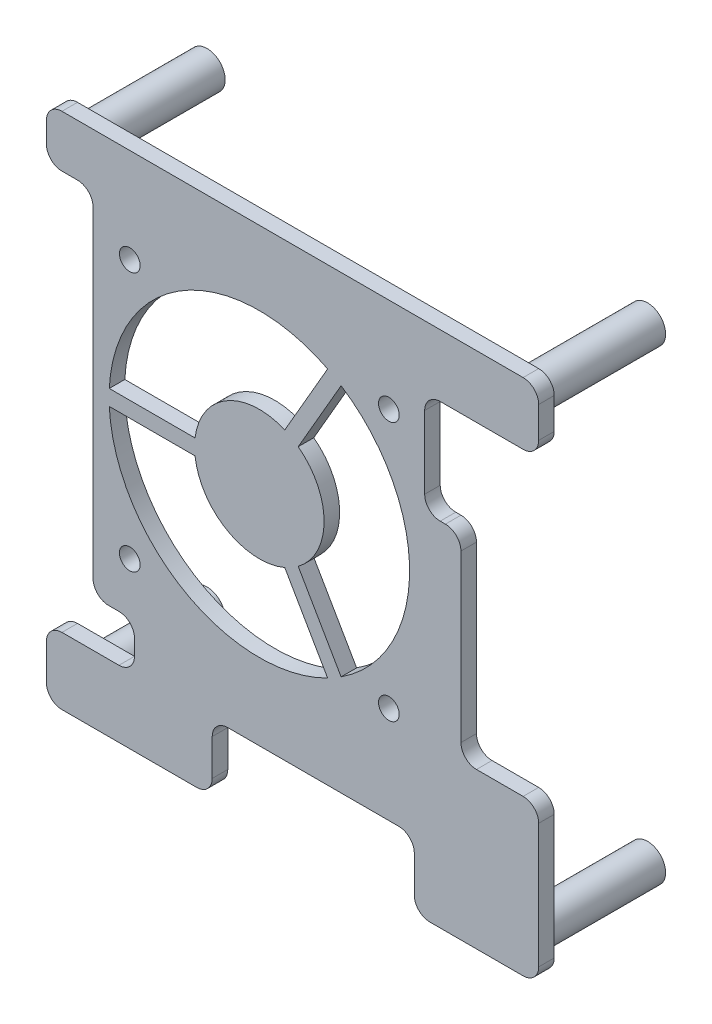
SolidWorks part; units mm, degrees
ref_plane "Alzado" through (0, 0, 0) normal (0, 0, 1) x (1, 0, 0)
ref_plane "Planta" through (0, 0, 0) normal (0, 1, 0) x (1, 0, 0)
ref_plane "Vista lateral" through (0, 0, 0) normal (1, 0, 0) x (0, 0, -1)
sketch "Croquis1" plane through (0, 0, 0) normal (0, 0, 1) x (1, 0, 0)
  line L0 (-194.105, 92.4709) -> (-194.105, 88.4709)
  line L1 (-191.105, 95.4709) -> (-102.105, 95.4709)
  line L2 (-99.105, 92.4709) -> (-99.105, 86.4709)
  line L3 (-140.5125, 52.2157) -> (-124.0125, 52.2157) construction
  line L4 (-102.105, -4.5291) -> (-120.105, -4.5291)
  line L5 (-194.105, 95.4709) -> (-99.105, -4.5291) construction
  line L6 (-194.105, -4.5291) -> (-99.105, 95.4709) construction
  line L7 (-191.105, 85.4709) -> (-188.105, 85.4709)
  line L8 (-185.105, 82.4709) -> (-185.105, 20.3828)
  line L9 (-182.105, 17.3828) -> (-180.105, 17.3828)
  line L10 (-177.105, 14.3828) -> (-177.105, 11.3828)
  line L11 (-180.105, 8.3828) -> (-191.105, 8.3828)
  line L12 (-194.105, 5.3828) -> (-194.105, -1.5291)
  line L13 (-102.105, 83.4709) -> (-118.105, 83.4709)
  line L14 (-121.105, 80.4709) -> (-121.105, 66.4709)
  line L15 (-118.105, 63.4709) -> (-117.105, 63.4709)
  line L16 (-114.105, 60.4709) -> (-114.105, 28.4709)
  line L17 (-111.105, 25.4709) -> (-102.105, 25.4709)
  line L18 (-99.105, 22.4709) -> (-99.105, -1.5291)
  line L19 (-123.105, -1.5291) -> (-123.105, 5.4709)
  line L20 (-126.105, 8.4709) -> (-159.105, 8.4709)
  line L21 (-162.105, 5.4709) -> (-162.105, -1.5291)
  line L22 (-165.105, -4.5291) -> (-191.105, -4.5291)
  line L27 (-183.0125, 82.2157) -> (-123.0125, 22.2157) construction
  line L28 (-183.0125, 22.2157) -> (-123.0125, 82.2157) construction
  line L29 (-132.2625, 52.2157) -> (-132.2625, 53.7157) construction
  line L30 (-165.4222, 50.7157) -> (-181.9737, 50.7157)
  line L31 (-132.2625, 52.2157) -> (-132.2625, 50.7157) construction
  line L32 (-165.4222, 53.7157) -> (-181.9737, 53.7157)
  line L33 (-145.5086, 62.2128) -> (-137.2329, 76.5468)
  line L34 (-148.1067, 63.7128) -> (-139.831, 78.0468)
  line L35 (-148.1067, 40.7186) -> (-139.831, 26.3846)
  line L36 (-145.5086, 42.2186) -> (-137.2329, 27.8846)
  arc A0 (-194.105, 92.4709) -> (-191.105, 95.4709) centre (-191.105, 92.4709) cw
  arc A1 (-194.105, 88.4709) -> (-191.105, 85.4709) centre (-191.105, 88.4709) ccw
  arc A2 (-185.105, 82.4709) -> (-188.105, 85.4709) centre (-188.105, 82.4709) ccw
  arc A3 (-182.105, 17.3828) -> (-185.105, 20.3828) centre (-182.105, 20.3828) cw
  arc A4 (-177.105, 14.3828) -> (-180.105, 17.3828) centre (-180.105, 14.3828) ccw
  arc A5 (-177.105, 11.3828) -> (-180.105, 8.3828) centre (-180.105, 11.3828) cw
  arc A6 (-191.105, 8.3828) -> (-194.105, 5.3828) centre (-191.105, 5.3828) ccw
  arc A7 (-194.105, -1.5291) -> (-191.105, -4.5291) centre (-191.105, -1.5291) ccw
  arc A8 (-162.105, -1.5291) -> (-165.105, -4.5291) centre (-165.105, -1.5291) cw
  arc A9 (-159.105, 8.4709) -> (-162.105, 5.4709) centre (-159.105, 5.4709) ccw
  arc A10 (-123.105, 5.4709) -> (-126.105, 8.4709) centre (-126.105, 5.4709) ccw
  arc A11 (-120.105, -4.5291) -> (-123.105, -1.5291) centre (-120.105, -1.5291) cw
  arc A12 (-102.105, -4.5291) -> (-99.105, -1.5291) centre (-102.105, -1.5291) ccw
  arc A13 (-102.105, 25.4709) -> (-99.105, 22.4709) centre (-102.105, 22.4709) cw
  arc A14 (-114.105, 28.4709) -> (-111.105, 25.4709) centre (-111.105, 28.4709) ccw
  arc A15 (-117.105, 63.4709) -> (-114.105, 60.4709) centre (-117.105, 60.4709) cw
  arc A16 (-121.105, 66.4709) -> (-118.105, 63.4709) centre (-118.105, 66.4709) ccw
  arc A17 (-118.105, 83.4709) -> (-121.105, 80.4709) centre (-118.105, 80.4709) ccw
  arc A18 (-99.105, 86.4709) -> (-102.105, 83.4709) centre (-102.105, 86.4709) cw
  arc A19 (-102.105, 95.4709) -> (-99.105, 92.4709) centre (-102.105, 92.4709) cw
  arc A21 (-181.9737, 53.7157) -> (-139.831, 78.0468) centre (-153.0125, 52.2157) cw
  arc A22 (-165.4222, 53.7157) -> (-148.1067, 63.7128) centre (-153.0125, 52.2157) cw
  arc A23 (-145.5086, 62.2128) -> (-145.5086, 42.2186) centre (-153.0125, 52.2157) cw
  arc A24 (-148.1067, 40.7186) -> (-165.4222, 50.7157) centre (-153.0125, 52.2157) cw
  arc A25 (-137.2329, 76.5468) -> (-137.2329, 27.8846) centre (-153.0125, 52.2157) cw
  arc A26 (-139.831, 26.3846) -> (-181.9737, 50.7157) centre (-153.0125, 52.2157) cw
  point P0 (-146.605, 45.4709)
  point P65 (-153.0125, 52.2157)
  point P92 (-153.0125, 52.2157)
  dimension "D3" = 3
  dimension "D4" = 3
  dimension "D5" = 3
  dimension "D6" = 3
  dimension "D7" = 3
  dimension "D8" = 3
  dimension "D9" = 3
  dimension "D10" = 3
  dimension "D11" = 3
  dimension "D12" = 3
  dimension "D13" = 3
  dimension "D14" = 3
  dimension "D15" = 3
  dimension "D16" = 3
  dimension "D17" = 3
  dimension "D18" = 3
  dimension "D19" = 3
  dimension "D20" = 3
  dimension "D21" = 3
  dimension "D22" = 3
  dimension "D23" = 60
  dimension "D25" = 3
  dimension "D1" = 100
  dimension "D2" = 95
  dimension "D24" = 60
extrude "Saliente-Extruir1" add sketch "Croquis1" along normal blind 3
sketch "Croquis2" plane through (0, 0, 0) normal (0, 0, -1) x (-1, 0, 0)
  line L0 (194.105, 92.4709) -> (194.105, 88.4709) construction
  line L1 (102.105, 95.4709) -> (191.105, 95.4709) construction
  circle A0 centre (189.105, 90.4709) radius 3.5
  circle A1 centre (104.105, 90.4709) radius 3.5
  circle A2 centre (104.105, 0.4709) radius 3.5
  circle A3 centre (189.105, 0.4709) radius 3.5
  circle A4 centre (189.105, 90.4709) radius 1.5
  circle A5 centre (104.105, 90.4709) radius 1.5
  circle A6 centre (104.105, 0.4709) radius 1.5
  circle A7 centre (189.105, 0.4709) radius 1.5
  dimension "D1" = 5
  dimension "D5" = 2
  dimension "D2" = 5
  dimension "D3" = 2
  dimension "D4" = 2
  dimension "D6" = 2
extrude "Saliente-Extruir2" add sketch "Croquis2" along normal blind 23
sketch "Croquis3" plane through (0, 0, 3) normal (0, 0, 1) x (1, 0, 0)
  line L5 (-123.0125, 22.2157) -> (-183.0125, 82.2157) construction
  line L6 (-123.0125, 82.2157) -> (-183.0125, 22.2157) construction
  circle A0 centre (-178.0125, 77.2157) radius 2
  circle A1 centre (-128.0125, 77.2157) radius 2
  circle A2 centre (-128.0125, 27.2157) radius 2
  circle A3 centre (-178.0125, 27.2157) radius 2
  point P0 (-153.0125, 52.2157)
  dimension "D1" = 60
  dimension "D2" = 60
  dimension "D4" = 2
  dimension "D5" = 2
extrude "Cortar-Extruir1" cut sketch "Croquis3" against normal up to vertex (3 mm away)
